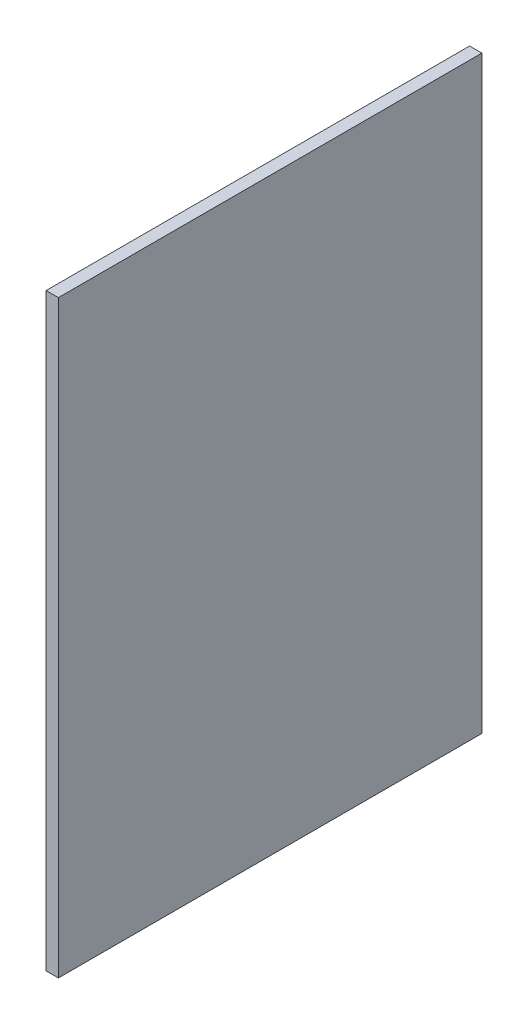
SolidWorks part; units mm, degrees
ref_plane "Front Plane" through (0, 0, 0) normal (0, 0, 1) x (1, 0, 0)
ref_plane "Top Plane" through (0, 0, 0) normal (0, 1, 0) x (1, 0, 0)
ref_plane "Right Plane" through (0, 0, 0) normal (1, 0, 0) x (0, 0, -1)
sketch "Sketch1" plane through (0, 0, 0) normal (1, 0, 0) x (0, 0, -1)
  line L1 (0, 0) -> (876.3, 0)
  line L2 (0, 0) -> (0, -1219.2)
  line L3 (0, -1219.2) -> (876.3, -1219.2)
  line L4 (876.3, 0) -> (876.3, -1219.2)
  dimension "D1" = 1219.2
  dimension "D2" = 876.3
extrude "Boss-Extrude1" add sketch "Sketch1" along normal blind 25.4
